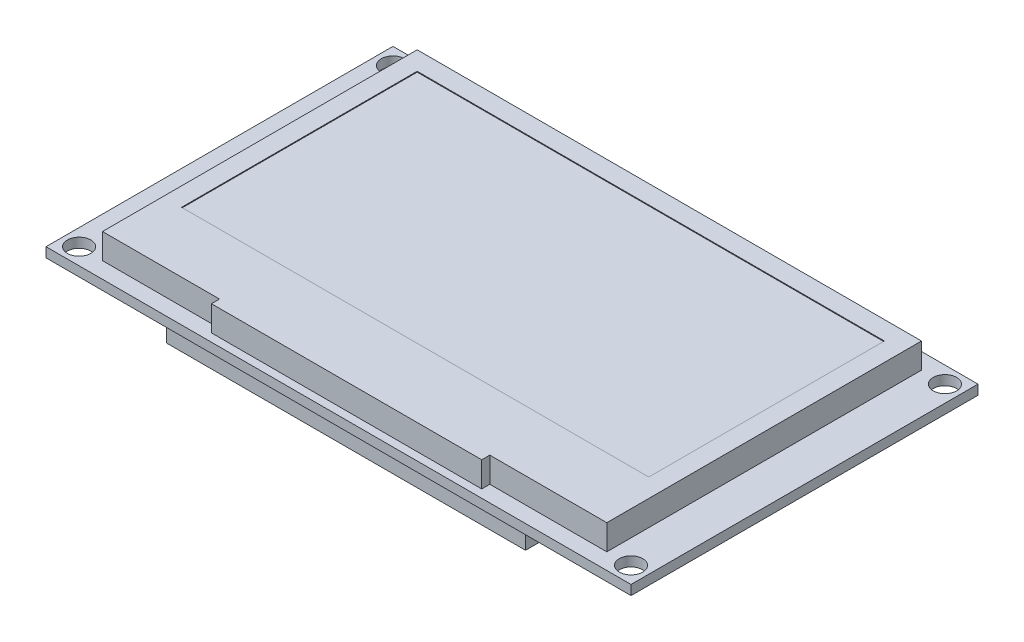
SolidWorks part; units mm, degrees
ref_plane "Front Plane" through (0, 0, 0) normal (0, 0, 1) x (1, 0, 0)
ref_plane "Top Plane" through (0, 0, 0) normal (0, 1, 0) x (1, 0, 0)
ref_plane "Right Plane" through (0, 0, 0) normal (1, 0, 0) x (0, 0, -1)
sketch "Sketch1" plane through (0, 0, 0) normal (0, 1, 0) x (1, 0, 0)
  line L0 (-36.25, 0) -> (0, 0) construction
  line L1 (-36.25, -21.5) -> (36.25, -21.5)
  line L2 (-36.25, -21.5) -> (-36.25, 21.5)
  line L3 (-36.25, 21.5) -> (36.25, 21.5)
  line L4 (36.25, -21.5) -> (36.25, 21.5)
  line L5 (-36.25, -21.5) -> (36.25, 21.5) construction
  line L6 (-36.25, 21.5) -> (36.25, -21.5) construction
  line L7 (0, 0) -> (0, 21.5) construction
  line L8 (-36.25, 21.5) -> (-34.2, 19.45) construction
  circle A0 centre (-34.2, 19.45) radius 1.45
  circle A1 centre (-33.75, 7.62) radius 0.5
  circle A2 centre (-33.75, 5.08) radius 0.5
  circle A3 centre (-33.75, 2.54) radius 0.5
  circle A4 centre (-33.75, 0) radius 0.5
  circle A5 centre (-33.75, -2.54) radius 0.5
  circle A6 centre (-33.75, -5.08) radius 0.5
  circle A7 centre (-33.75, -7.62) radius 0.5
  circle A8 centre (-34.2, -19.45) radius 1.45
  circle A9 centre (34.2, 19.45) radius 1.45
  circle A10 centre (34.2, -19.45) radius 1.45
  point P0 (0, 0)
  point P11 (-34.2, 18)
  point P14 (-33.75, 0)
  dimension "D5" = 2.9
  dimension "D6" = 1
  dimension "D1" = 72.5
  dimension "D2" = 43
  dimension "D3" = 45
  dimension "D4" = 36
  dimension "D8" = 2.5
  dimension "D9" = 2.54
  dimension "D7" = 7
extrude "Boss-Extrude1" add sketch "Sketch1" against normal blind 1.2
sketch "Sketch2" plane through (0, -1.2, 0) normal (0, -1, 0) x (1, 0, 0)
  line L0 (-36.25, -21.5) -> (-36.25, 21.5) construction
  line L1 (-22.25, -20.573) -> (22.25, -20.573)
  line L2 (-22.25, -20.573) -> (-22.25, 20.573)
  line L3 (-22.25, 20.573) -> (22.25, 20.573)
  line L4 (22.25, -20.573) -> (22.25, 20.573)
  line L5 (-22.25, -20.573) -> (22.25, 20.573) construction
  line L6 (-22.25, 20.573) -> (22.25, -20.573) construction
  point P0 (0, 0)
  dimension "D1" = 14
extrude "Boss-Extrude2" add sketch "Sketch2" along normal blind 2.6
sketch "Sketch3" plane through (0, 0, 0) normal (0, 1, 0) x (1, 0, 0)
  line L0 (-16.75, -19.5) -> (-16.75, -20.5)
  line L1 (-31.25, -19.5) -> (-16.75, -19.5)
  line L2 (-31.25, -19.5) -> (-31.25, 19.5)
  line L3 (-31.25, 19.5) -> (31.25, 19.5)
  line L4 (31.25, -19.5) -> (31.25, 19.5)
  line L5 (-31.25, -19.5) -> (31.25, 19.5) construction
  line L6 (-31.25, 19.5) -> (31.25, -19.5) construction
  line L7 (-16.75, -20.5) -> (16.75, -20.5)
  line L8 (16.75, -20.5) -> (16.75, -19.5)
  line L9 (16.75, -19.5) -> (31.25, -19.5)
  point P0 (0, 0)
  point P10 (0, -20.5)
  dimension "D1" = 62.5
  dimension "D2" = 39
  dimension "D3" = 40
  dimension "D4" = 33.5
extrude "Boss-Extrude3" add sketch "Sketch3" along normal blind 3.13
sketch "Sketch4" plane through (0, 3.13, 0) normal (0, 1, 0) x (1, 0, 0)
  line L0 (31.25, 19.5) -> (-31.25, 19.5) construction
  line L1 (-28.95, -12) -> (28.95, -12)
  line L2 (-28.95, -12) -> (-28.95, 17.2)
  line L3 (-28.95, 17.2) -> (28.95, 17.2)
  line L4 (28.95, -12) -> (28.95, 17.2)
  line L5 (-28.95, -12) -> (28.95, 17.2) construction
  line L6 (-28.95, 17.2) -> (28.95, -12) construction
  line L7 (31.25, -19.5) -> (31.25, 19.5) construction
  line L8 (16.75, -19.5) -> (31.25, -19.5) construction
  point P0 (0, 2.6)
  point P9 (0, 0)
  dimension "D1" = 2.3
  dimension "D2" = 2.3
  dimension "D3" = 7.5
extrude "Cut-Extrude1" cut sketch "Sketch4" against normal blind 0.1
